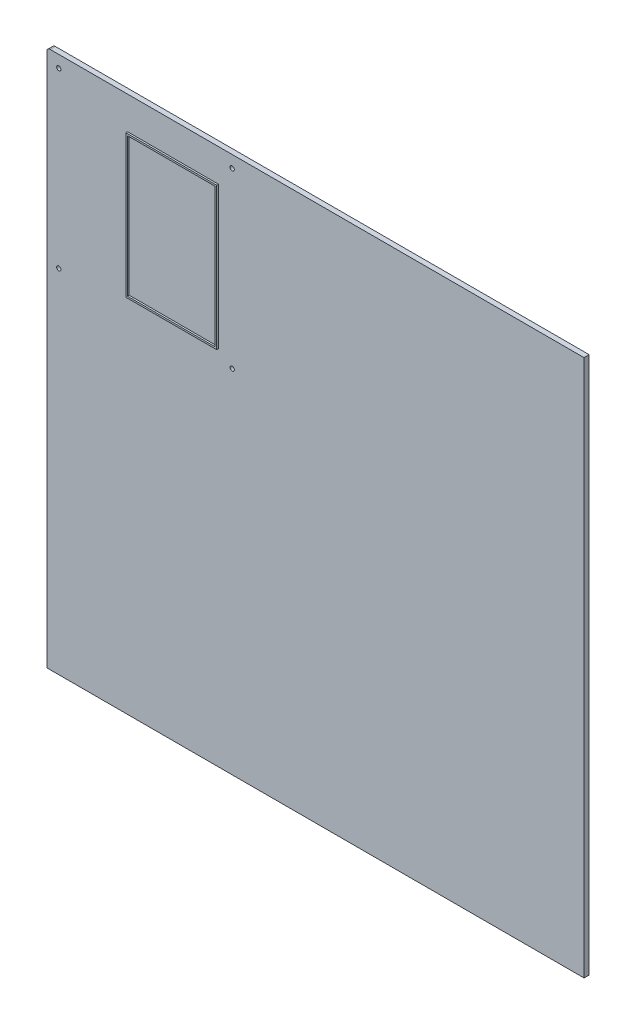
SolidWorks part; units mm, degrees
ref_plane "Plan de face" through (0, 0, 0) normal (0, 0, 1) x (1, 0, 0)
ref_plane "Plan de dessus" through (0, 0, 0) normal (0, 1, 0) x (1, 0, 0)
ref_plane "Plan de droite" through (0, 0, 0) normal (1, 0, 0) x (0, 0, -1)
sketch "Esquisse1" plane through (0, 0, 0) normal (0, 0, 1) x (1, 0, 0)
  line L1 (-143.1506, 111.4684) -> (86.8494, 111.4684)
  line L2 (-143.1506, 111.4684) -> (-143.1506, -118.5316)
  line L3 (-143.1506, -118.5316) -> (86.8494, -118.5316)
  line L4 (86.8494, 111.4684) -> (86.8494, -118.5316)
  line L5 (-129.1506, 97.4684) -> (72.8494, 97.4684) construction
  line L6 (-129.1506, 97.4684) -> (-129.1506, -104.5316) construction
  line L7 (-129.1506, -104.5316) -> (72.8494, -104.5316) construction
  line L8 (72.8494, 97.4684) -> (72.8494, -104.5316) construction
  line L9 (-129.1506, 97.4684) -> (72.8494, -104.5316) construction
  line L10 (-129.1506, -104.5316) -> (72.8494, 97.4684) construction
  circle A0 centre (-129.1506, 97.4684) radius 2.5
  circle A1 centre (72.8494, 97.4684) radius 2.5
  circle A2 centre (72.8494, -104.5316) radius 2.5
  circle A3 centre (-129.1506, -104.5316) radius 2.5
  point P8 (-28.1506, -3.5316)
  point P19 (-28.1506, -3.5316)
  dimension "D7" = 5
  dimension "D1" = 230
  dimension "D2" = 230
  dimension "D3" = 202
  dimension "D4" = 202
  dimension "D5" = 14
  dimension "D6" = 14
  dimension "D8" = 4
extrude "Boss.-Extru.1" add sketch "Esquisse1" along normal blind 6
fillet "Congé1" radius 4 4 edges at (-143.1506, -118.5316, 3) (86.8494, -118.5316, 3) (-143.1506, 111.4684, 3) (86.8494, 111.4684, 3)
sketch "Esquisse2" plane through (0, 0, 6) normal (0, 0, 1) x (1, 0, 0)
  line L0 (86.8494, -114.5316) -> (86.8494, 107.4684) construction
  line L1 (-47.1506, 71.4684) -> (54.8494, 71.4684)
  line L2 (-47.1506, 71.4684) -> (-47.1506, -90.5316)
  line L3 (-47.1506, -90.5316) -> (54.8494, -90.5316)
  line L4 (54.8494, 71.4684) -> (54.8494, -90.5316)
  line L5 (-47.1506, 71.4684) -> (54.8494, -90.5316) construction
  line L6 (-47.1506, -90.5316) -> (54.8494, 71.4684) construction
  line L7 (-49.1506, 73.4684) -> (56.8494, 73.4684)
  line L8 (-49.1506, 73.4684) -> (-49.1506, -92.5316)
  line L9 (-49.1506, -92.5316) -> (56.8494, -92.5316)
  line L10 (56.8494, 73.4684) -> (56.8494, -92.5316)
  line L11 (-49.1506, 73.4684) -> (56.8494, -92.5316) construction
  line L12 (-49.1506, -92.5316) -> (56.8494, 73.4684) construction
  line L13 (82.8494, 111.4684) -> (-139.1506, 111.4684) construction
  point P4 (3.8494, -9.5316)
  point P9 (3.8494, -9.5316)
  dimension "D1" = 106
  dimension "D2" = 166
  dimension "D3" = 102
  dimension "D4" = 162
  dimension "D5" = 2
  dimension "D6" = 2
  dimension "D7" = 30
  dimension "D8" = 38
extrude "Boss.-Extru.2" add sketch "Esquisse2" along normal blind 2 contours L8 L7 L10 L9 | L2 L1 L4 L3
sketch "Esquisse3" plane through (0, 0, 0) normal (0, 0, -1) x (-1, 0, 0)
  line L0 (-82.8494, 111.4684) -> (-482.8494, 111.4684)
  line L1 (-482.8494, 111.4684) -> (-482.8494, -514.5316)
  line L2 (-482.8494, -514.5316) -> (143.1506, -514.5316)
  line L3 (143.1506, -114.5316) -> (143.1506, -514.5316)
  line L4 (143.1506, 107.4684) -> (143.1506, -114.5316) construction
  line L5 (-82.8494, 111.4684) -> (-82.8494, -114.5316)
  line L6 (-82.8494, -114.5316) -> (143.1506, -114.5316)
  dimension "D1" = 400
extrude "Boss.-Extru.3" add sketch "Esquisse3" against normal blind 6
